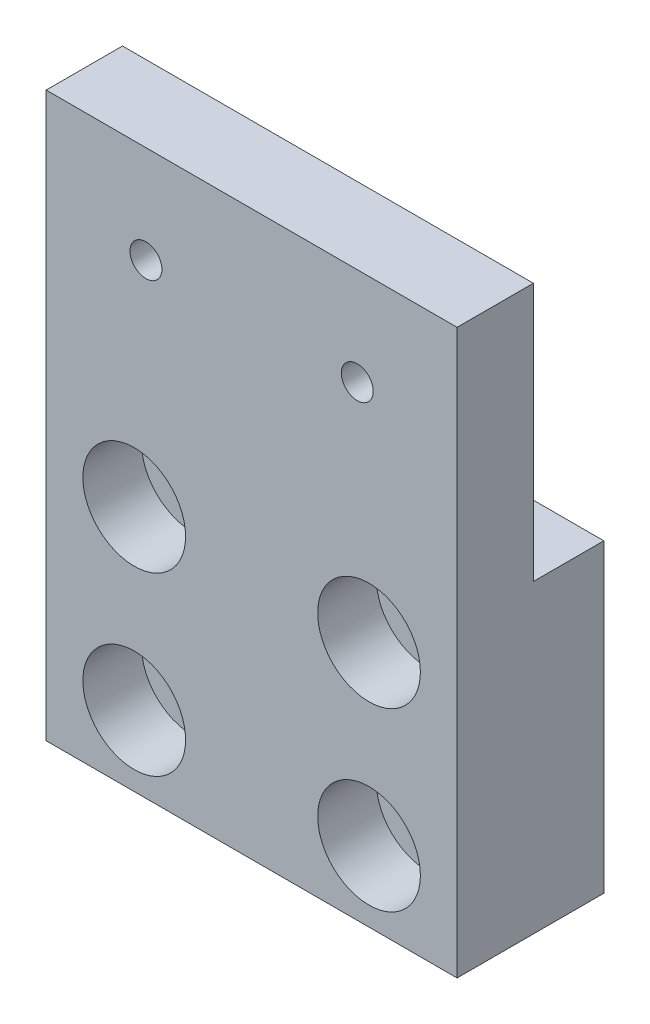
SolidWorks part; units mm, degrees
ref_plane "Front Plane" through (0, 0, 0) normal (0, 0, 1) x (1, 0, 0)
ref_plane "Top Plane" through (0, 0, 0) normal (0, 1, 0) x (1, 0, 0)
ref_plane "Right Plane" through (0, 0, 0) normal (1, 0, 0) x (0, 0, -1)
sketch "Sketch1" plane through (0, 0, 0) normal (0, 0, 1) x (1, 0, 0)
  line L1 (-22.225, 30.48) -> (22.225, 30.48)
  line L2 (-22.225, 30.48) -> (-22.225, -30.48)
  line L3 (-22.225, -30.48) -> (22.225, -30.48)
  line L4 (22.225, 30.48) -> (22.225, -30.48)
  dimension "D1" = 22.225
  dimension "D2" = 22.225
  dimension "D3" = 30.48
  dimension "D4" = 30.48
extrude "Boss-Extrude1" add sketch "Sketch1" along normal mid plane 15.875
hole_wizard "CBORE for 1/4 Socket Head Cap Screw1" positions "Sketch3" profile "Sketch2" counterbore size "1/4" standard "ANSI Inch" end condition through all
sketch "Sketch3" plane through (0, 0, 7.9375) normal (0, 0, 1) x (1, 0, 0)
  line L0 (-22.225, -30.48) -> (22.225, -30.48) construction
  point P0 (-12.7, -3.81)
  point P2 (12.7, -3.81)
  point P4 (12.7, -22.86)
  point P6 (-12.7, -22.86)
  dimension "D1" = 19.05
  dimension "D2" = 7.62
  dimension "D3" = 12.7
  dimension "D4" = 12.7
sketch "Sketch2" plane through (-12.7, -3.81, 7.9375) normal (1, 0, 0) x (0, -1, 0)
  line L0 (0, 0) -> (0, 15.875)
  line L1 (0, 15.875) -> (3.3782, 15.875)
  line L3 (3.3782, 15.875) -> (3.3782, 6.35)
  line L4 (3.3782, 6.35) -> (5.5562, 6.35)
  line L5 (5.5562, 6.35) -> (5.5562, 0)
  line L7 (5.5562, 0) -> (0, 0)
  line L11 (0, -6.35) -> (0, 107.95) construction
  dimension "Thru Hole Dia." = 6.7564
  dimension "Thru Hole Depth" = 15.875
  dimension "C'Bore Dia." = 11.1125
  dimension "C'Bore Depth" = 6.35
sketch "Sketch4" plane through (22.225, 0, 0) normal (1, 0, 0) x (0, 0, -1)
  line L1 (7.9375, 30.48) -> (0.3175, 30.48)
  line L2 (7.9375, 30.48) -> (7.9375, 2.54)
  line L3 (7.9375, 2.54) -> (0.3175, 2.54)
  line L4 (0.3175, 30.48) -> (0.3175, 2.54)
  dimension "D1" = 7.62
  dimension "D2" = 27.94
extrude "Cut-Extrude1" cut sketch "Sketch4" against normal through all
hole_wizard "#8-32 Tapped Hole1" positions "Sketch6" profile "Sketch5" tap size "#8-32" standard "ANSI Inch" end condition through all
sketch "Sketch6" plane through (0, 0, 7.9375) normal (0, 0, 1) x (1, 0, 0)
  circle A0 centre (12.7, -3.81) radius 3.3782 construction
  point P0 (-11.43, 19.939)
  point P2 (11.43, 19.939)
  dimension "D1" = 11.43
  dimension "D2" = 11.43
  dimension "D3" = 23.749
sketch "Sketch5" plane through (-11.43, 19.939, 7.9375) normal (1, 0, 0) x (0, -1, 0)
  line L0 (0, 0) -> (0, 15.875)
  line L1 (0, 15.875) -> (1.7272, 15.875)
  line L2 (1.7272, 15.875) -> (1.7272, 0)
  line L5 (1.7272, 0) -> (0, 0)
  line L11 (0, -6.35) -> (0, 107.95) construction
  dimension "Thru Tap Drill Dia." = 3.4544
  dimension "Thru Tap Drill Depth" = 15.875
cosmetic thread "Hole Thread1" parameters "D2"=4.1656
cosmetic thread "Hole Thread2" parameters "D2"=4.1656
